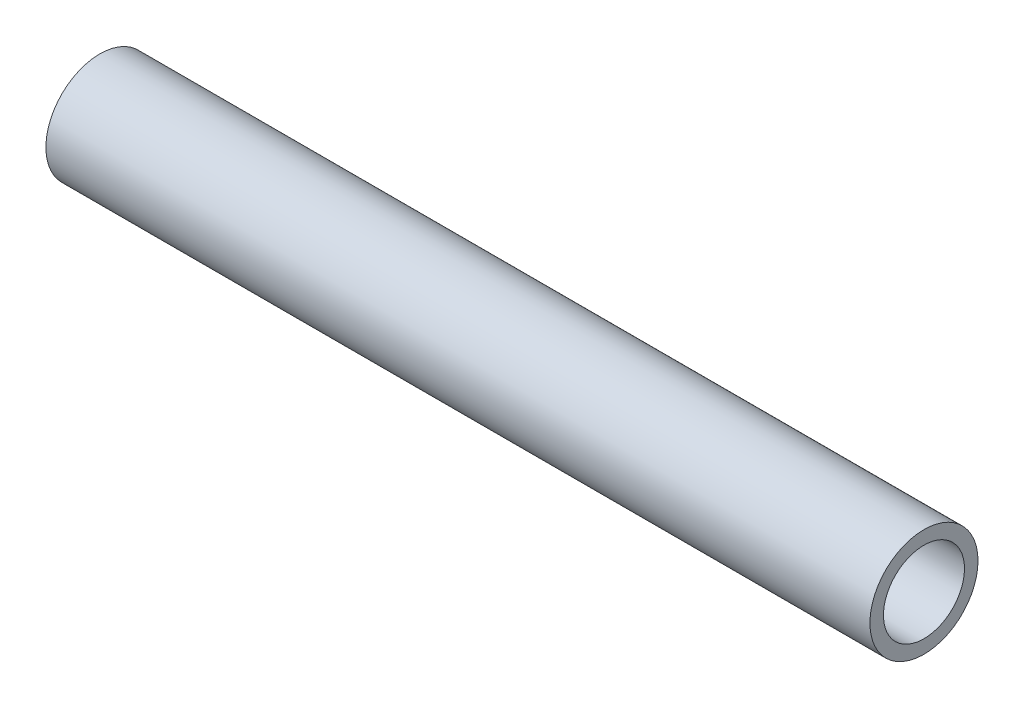
SolidWorks part; units mm, degrees
material "6061-T6 (SS)"
ref_plane "Front Plane" through (0, 0, 0) normal (0, 0, 1) x (1, 0, 0)
ref_plane "Top Plane" through (0, 0, 0) normal (0, 1, 0) x (1, 0, 0)
ref_plane "Right Plane" through (0, 0, 0) normal (1, 0, 0) x (0, 0, -1)
sketch "Sketch1" plane through (0, 0, 0) normal (1, 0, 0) x (0, 0, -1)
  circle A0 centre (0, 0) radius 12.7
  circle A1 centre (0, 0) radius 9.525
  dimension "D1" = 25.4
  dimension "D2" = 3.175
extrude "Boss-Extrude1" add sketch "Sketch1" along normal blind 193.675
